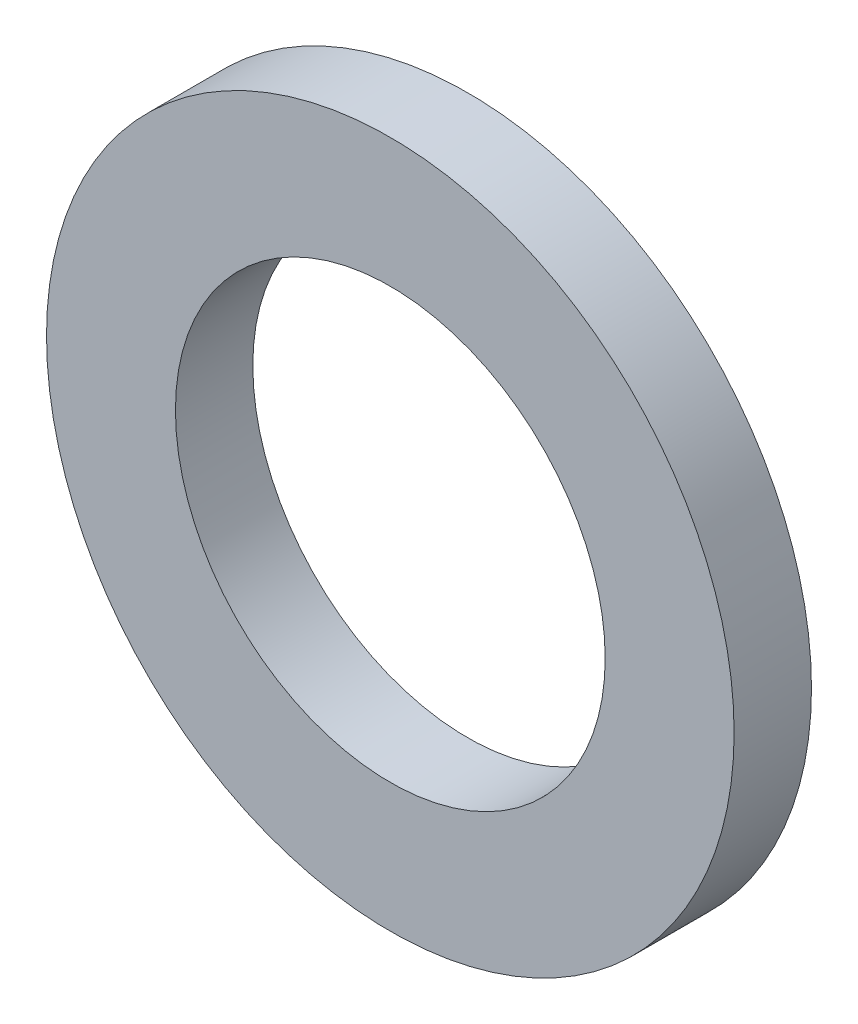
SolidWorks part; units mm, degrees
ref_plane "Front Plane" through (0, 0, 0) normal (0, 0, 1) x (1, 0, 0)
ref_plane "Top Plane" through (0, 0, 0) normal (0, 1, 0) x (1, 0, 0)
ref_plane "Right Plane" through (0, 0, 0) normal (1, 0, 0) x (0, 0, -1)
sketch "Sketch1" plane through (0, 0, 0) normal (0, 0, 1) x (1, 0, 0)
  circle A0 centre (0, 0) radius 12
  circle A1 centre (0, 0) radius 7.5
  point P5 (0, -12)
  dimension "OD" = 24
  dimension "ID" = 15
sketch "Sketch2" plane through (0, 0, 0) normal (1, 0, 0) x (0, 0, -1)
  line L0 (-1.35, 0) -> (1.35, 0) construction
  point P0 (-1.35, -12)
  point P4 (0, 0)
  point P6 (1.35, -12)
  dimension "Thickness Range" = 2.7
sketch "Sketch3" plane through (0, 0, 0) normal (0, 0, 1) x (1, 0, 0)
  circle A0 centre (0, 0) radius 12 construction
  circle A1 centre (0, 0) radius 7.5 construction
  circle A2 centre (0, 0) radius 12
  circle A3 centre (0, 0) radius 7.5
extrude "Boss-Extrude1" add sketch "Sketch3" along normal up to vertex (1.35 mm away) and the other way up to vertex (1.35 mm away) up to point (0, -12, 1.35) other way up to point (0, -12, -1.35)
